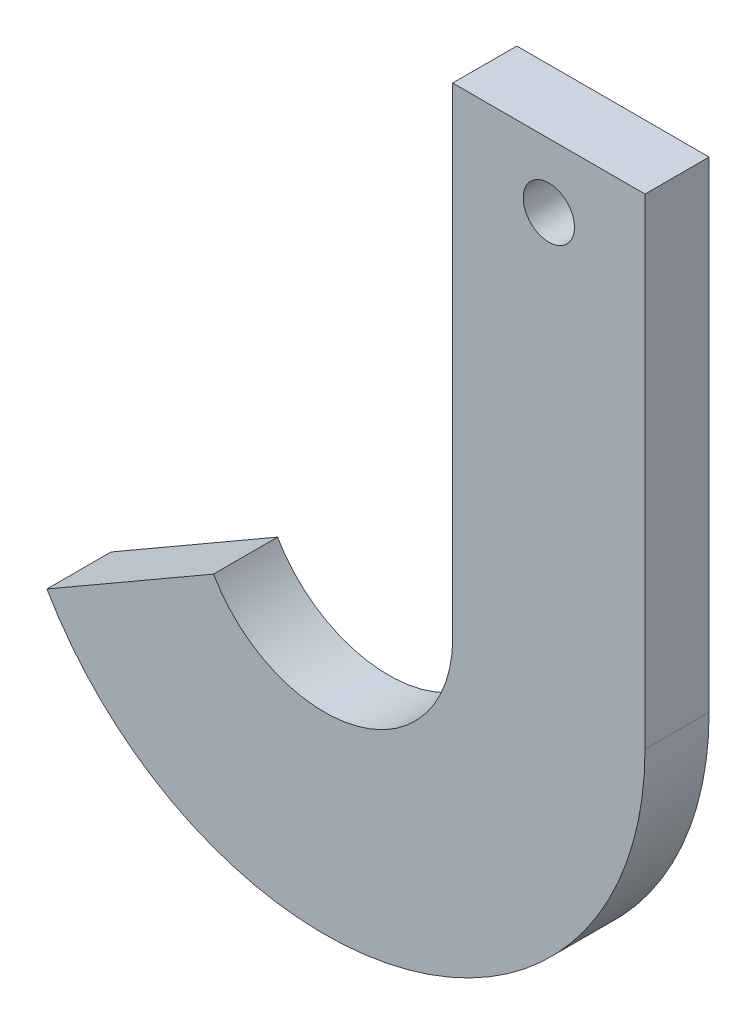
SolidWorks part; units mm, degrees
ref_plane "Front Plane" through (0, 0, 0) normal (0, 0, 1) x (1, 0, 0)
ref_plane "Top Plane" through (0, 0, 0) normal (0, 1, 0) x (1, 0, 0)
ref_plane "Right Plane" through (0, 0, 0) normal (1, 0, 0) x (0, 0, -1)
sketch "Sketch1" plane through (0, 0, 0) normal (0, 0, 1) x (1, 0, 0)
  line L0 (-34.641, -20) -> (-86.6025, -50)
  line L1 (100, 0) -> (100, 150)
  line L2 (40, 150) -> (40, 0)
  line L3 (40, 150) -> (100, 150)
  line L4 (0, 0) -> (-155.1085, 0) construction
  arc A0 (-34.641, -20) -> (40, 0) centre (0, 0) ccw
  arc A1 (-86.6025, -50) -> (100, 0) centre (0, 0) ccw
  dimension "D1" = 40
  dimension "D2" = 100
  dimension "D3" = 60
  dimension "D4" = 60
  dimension "D5" = 150
  dimension "D6" = 30
extrude "Extrude1" add sketch "Sketch1" along normal blind 20
sketch "Sketch2" plane through (0, 0, 0) normal (0, 0, 1) x (1, 0, 0)
  line L0 (100, 150) -> (40, 150) construction
  line L1 (40, 150) -> (40, 0) construction
  circle A0 centre (70, 130) radius 8
  dimension "D1" = 16
  dimension "D2" = 20
  dimension "D3" = 30
extrude "Extrude3" cut sketch "Sketch2" along normal through all
